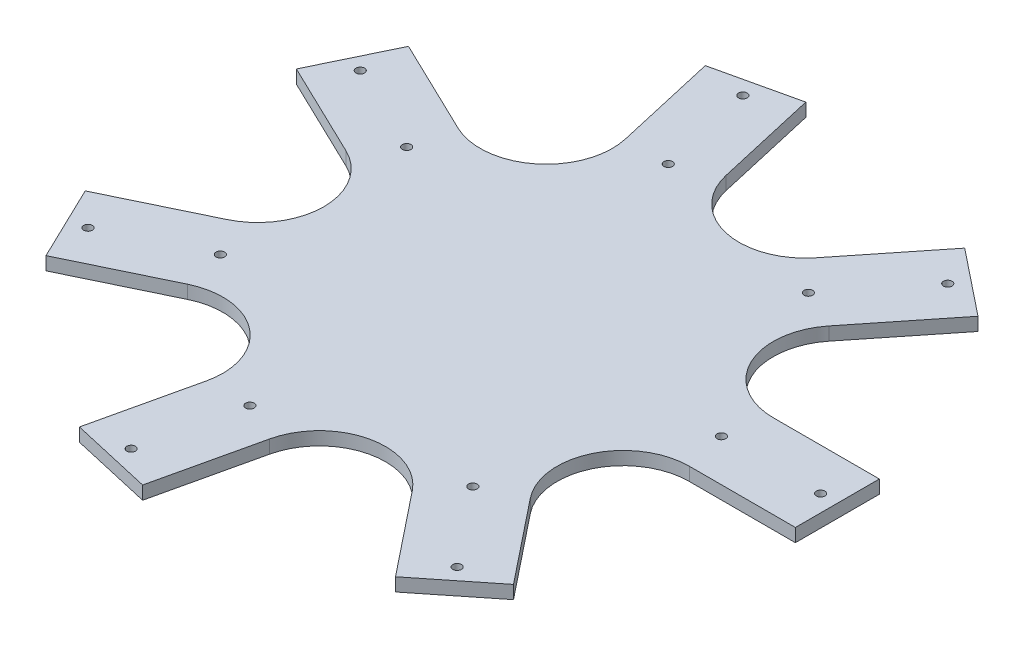
SolidWorks part; units mm, degrees
ref_plane "Front Plane" through (0, 0, 0) normal (0, 0, 1) x (1, 0, 0)
ref_plane "Top Plane" through (0, 0, 0) normal (0, 1, 0) x (1, 0, 0)
ref_plane "Right Plane" through (0, 0, 0) normal (1, 0, 0) x (0, 0, -1)
sketch "Sketch2" plane through (0, 0, 0) normal (0, 0, 1) x (1, 0, 0)
  line L0 (0, 0) -> (0, 63.9226) construction
sketch "Sketch3" plane through (0, 0, 0) normal (0, 1, 0) x (1, 0, 0)
  line L0 (0, 31.75) -> (0, -31.75)
  line L1 (0, 31.75) -> (250, 31.75)
  line L2 (0, -31.75) -> (250, -31.75)
  line L3 (250, 31.75) -> (250, -31.75)
  line L4 (0, 0) -> (-515.3919, 0) construction
  circle A0 centre (162.3, 0) radius 3.25
  circle A2 centre (237.3, 0) radius 3.25
  point P3 (0, 0)
  point P10 (0, 0)
  dimension "D6" = 6.5
  dimension "D1" = 63.5
  dimension "D2" = 12.7
  dimension "D3" = 250
  dimension "D4" = 75
extrude "Boss-Extrude1" add sketch "Sketch3" along normal blind 10
pattern_circular "CirPattern1" count 7 every 51.429 about axis through (0, 0, 0) along (0, 1, 0) of "Boss-Extrude1"
fillet "Fillet1" radius 50 7 edges at (65.9296, 5, 31.75) (16.2833, 5, 71.3416) (-45.6247, 5, 57.2115) (-73.1763, 5, 0) (-45.6247, 5, -57.2115) (16.2833, 5, -71.3416) (65.9296, 5, -31.75)
